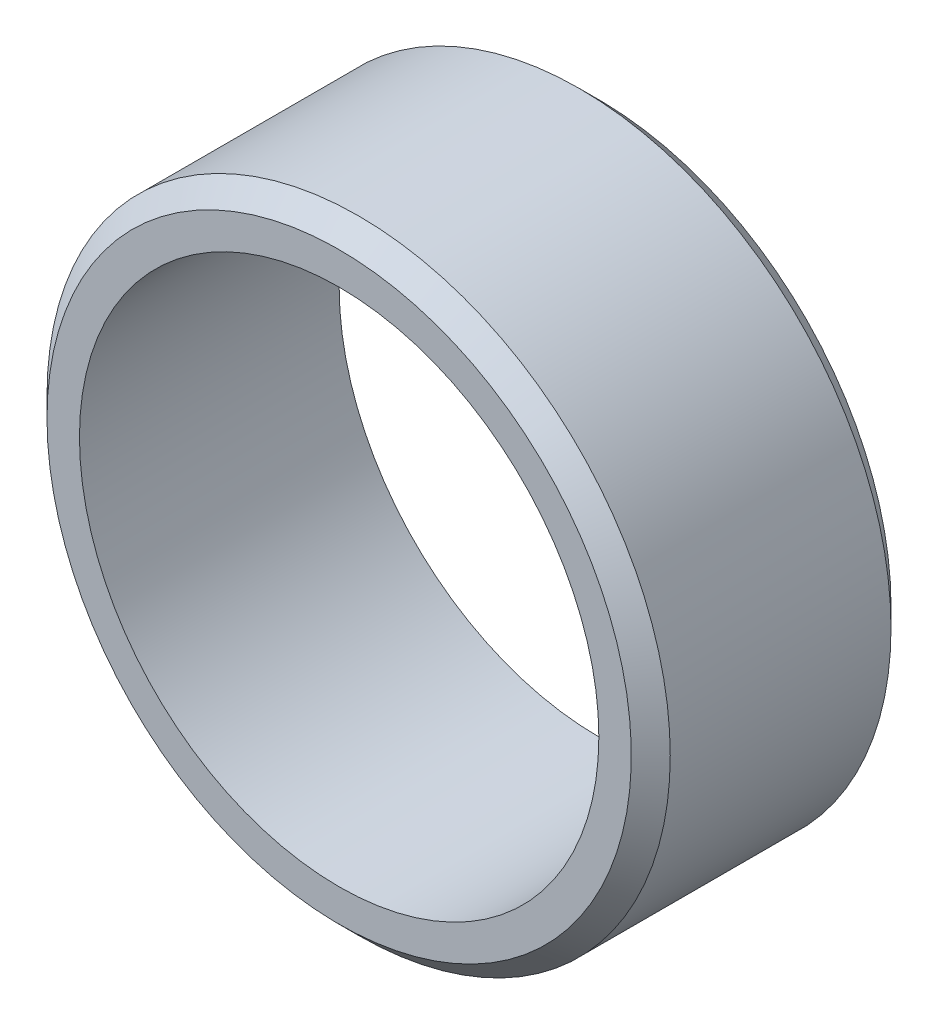
SolidWorks part; units mm, degrees
material "Nylon 101"
ref_plane "Front Plane" through (0, 0, 0) normal (0, 0, 1) x (1, 0, 0)
ref_plane "Top Plane" through (0, 0, 0) normal (0, 1, 0) x (1, 0, 0)
ref_plane "Right Plane" through (0, 0, 0) normal (1, 0, 0) x (0, 0, -1)
sketch "Sketch1" plane through (0, 0, 0) normal (1, 0, 0) x (0, 0, -1)
  line L0 (-12.5, 0) -> (12.5, 0) construction
  line L1 (12.5, 30) -> (12.5, -30) construction
  line L2 (-12.5, 30) -> (-12.5, -30) construction
  line L3 (12.5, 30) -> (-12.5, 30) construction
  line L4 (12.5, -30) -> (-12.5, -30) construction
  line L5 (-12.5, 25) -> (12.5, 25) construction
  line L6 (-12.5, -25) -> (12.5, -25) construction
  point P2 (0, 0)
  point P7 (-12.5, 0)
  point P8 (-12.5, -25)
  point P9 (12.5, 0)
  point P11 (-12.5, 25)
  dimension "OD" = 60
  dimension "ID" = 50
  dimension "Length" = 25
sketch "Sketch2" plane through (0, 0, 0) normal (0, 0, 1) x (1, 0, 0)
  line L0 (-30, 0) -> (30, 0) construction
  line L1 (0, -30) -> (0, 30) construction
  circle A0 centre (0, 0) radius 25 construction
  circle A1 centre (0, 0) radius 30 construction
  point P16 (0, 0)
  dimension "ID" = 50
  dimension "OD" = 60
sketch "Sketch3" plane through (0, 0, 0) normal (1, 0, 0) x (0, 0, -1)
  line L0 (-12.5, 25) -> (12.5, 25)
  line L1 (12.5, 30) -> (12.5, -30) construction
  line L2 (12.5, 25) -> (12.5, 30)
  line L5 (12.5, 30) -> (-12.5, 30)
  line L6 (-12.5, 30) -> (-12.5, 25)
  line L7 (-12.5, 0) -> (12.5, 0) construction
revolve "Revolve1" add sketch "Sketch3" angle 360 about L7
chamfer "Chamfer1" distance 1.875 angle 45 2 edges at (30, 0, 12.5) (30, 0, -12.5)
equation "\"D1@Chamfer1\"=((\"OD@Sketch1\"-\"ID@Sketch1\")/2)*.375"
